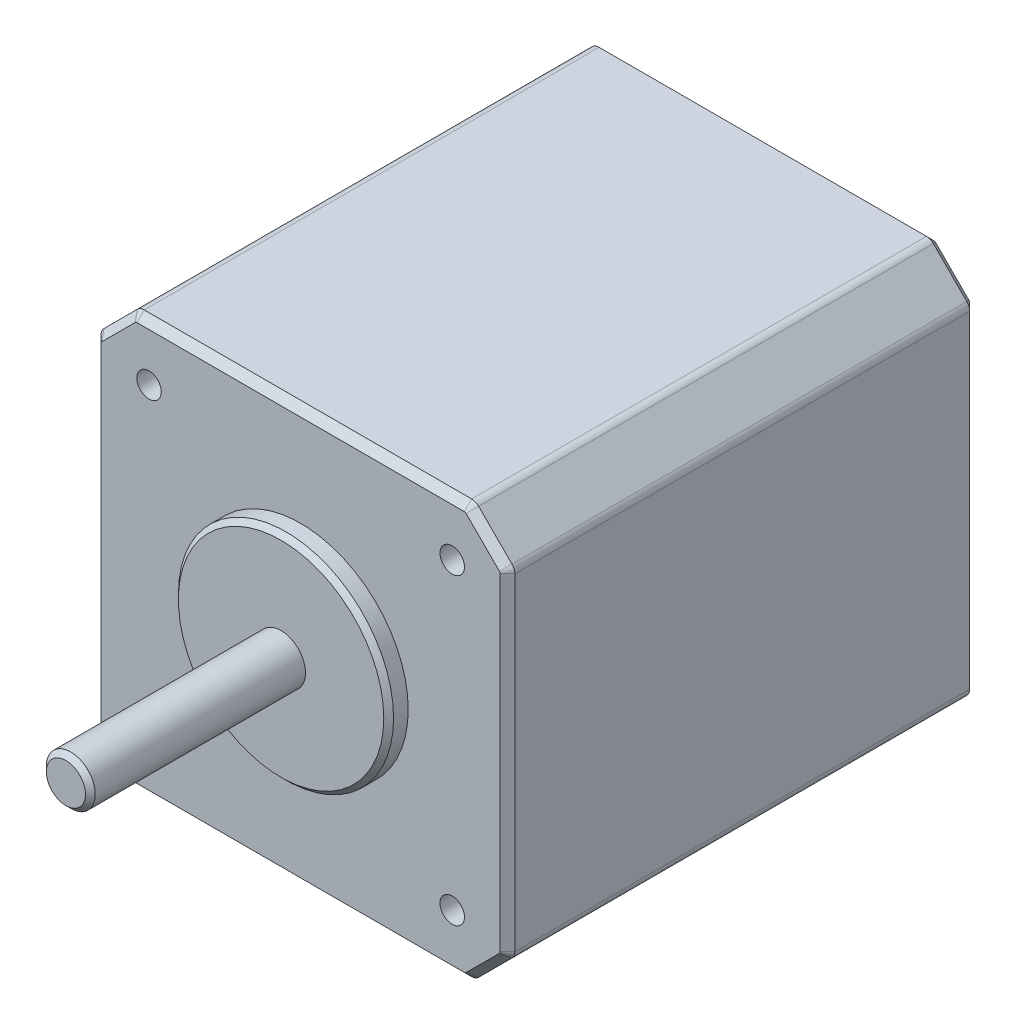
SolidWorks part; units mm, degrees
ref_plane "Спереди" through (0, 0, 0) normal (0, 0, 1) x (1, 0, 0)
ref_plane "Сверху" through (0, 0, 0) normal (0, 1, 0) x (1, 0, 0)
ref_plane "Справа" through (0, 0, 0) normal (1, 0, 0) x (0, 0, -1)
sketch "Sketch1" plane through (0, 0, 0) normal (0, 0, 1) x (1, 0, 0)
  line L1 (-21.15, -21.15) -> (21.15, -21.15)
  line L2 (-21.15, -21.15) -> (-21.15, 21.15)
  line L3 (-21.15, 21.15) -> (21.15, 21.15)
  line L4 (21.15, -21.15) -> (21.15, 21.15)
  line L5 (-21.15, -21.15) -> (21.15, 21.15) construction
  line L6 (-21.15, 21.15) -> (21.15, -21.15) construction
  line L11 (-15.5, -15.5) -> (15.5, 15.5) construction
  line L12 (-15.5, 15.5) -> (15.5, -15.5) construction
  point P0 (0, 0)
  point P6 (0, 0)
  point P12 (-15.5, 15.5)
  point P13 (15.5, 15.5)
  point P14 (15.5, -15.5)
  point P15 (-15.5, -15.5)
extrude "Boss-Extrude1" add sketch "Sketch1" against normal blind 48
hole_wizard "M3x0.5 Tapped Hole1" positions "Sketch5" profile "Sketch4" tap size "M3x0.5" standard "ANSI Metric"
sketch "Sketch5" plane through (0, 0, 0) normal (0, 0, 1) x (1, 0, 0)
  point P0 (-15.5, 15.5)
  point P3 (15.5, 15.5)
  point P6 (15.5, -15.5)
  point P9 (-15.5, -15.5)
sketch "Sketch4" plane through (-15.5, 15.5, 0) normal (1, 0, 0) x (0, -1, 0)
  line L0 (0, 0) -> (0, 6.7511)
  line L1 (0, 6.7511) -> (1.25, 6)
  line L2 (1.25, 6) -> (1.25, 0)
  line L5 (1.25, 0) -> (0, 0)
  line L10 (0, 6.7511) -> (-1.25, 6) construction
  line L11 (0, -6.35) -> (0, 107.95) construction
  dimension "Tap Drill Dia." = 2.5
  dimension "Tap Drill Depth" = 6
  dimension "Drill Angle" = 118
cosmetic thread "Hole Thread1" parameters "D1"=4.5, "D2"=3
cosmetic thread "Hole Thread2" parameters "D1"=4.5, "D2"=3
cosmetic thread "Hole Thread3" parameters "D1"=4.5, "D2"=3
cosmetic thread "Hole Thread4" parameters "D1"=4.5, "D2"=3
chamfer "Chamfer1" distance 4 angle 45 4 edges at (-21.15, -21.15, -24) (21.15, -21.15, -24) (21.15, 21.15, -24) (-21.15, 21.15, -24)
fillet "Fillet1" radius 1 8 edges at (-21.15, -17.15, -24) (-17.15, -21.15, -24) (17.15, -21.15, -24) (21.15, -17.15, -24) (21.15, 17.15, -24) (17.15, 21.15, -24) (-17.15, 21.15, -24) (-21.15, 17.15, -24)
sketch "Sketch6" plane through (0, 0, 0) normal (0, 0, 1) x (1, 0, 0)
  circle A0 centre (0, 0) radius 11
extrude "Boss-Extrude2" add sketch "Sketch6" along normal blind 2
sketch "Sketch7" plane through (0, 0, 2) normal (0, 0, 1) x (1, 0, 0)
  line L0 (-21.15, -21.15) -> (21.15, 21.15) construction
  circle A0 centre (0, 0) radius 2.5
extrude "Boss-Extrude3" add sketch "Sketch7" along normal blind 22
chamfer "Chamfer2" distance 0.5 angle 45 1 edges at (2.5, 0, 24)
chamfer "Chamfer3" distance 0.75 angle 45 16 edges at (0, -21.15, 0) (17.1185, -21.0739, 0) (-17.1185, -21.0739, 0) (19.15, -19.15, 0) (-19.15, -19.15, 0) (21.0739, -17.1185, 0) (-21.0739, -17.1185, 0) (21.15, 0, 0) (-21.15, 0, 0) (21.0739, 17.1185, 0) (-21.0739, 17.1185, 0) (19.15, 19.15, 0) (-19.15, 19.15, 0) (17.1185, 21.0739, 0) (-17.1185, 21.0739, 0) (0, 21.15, 0)
chamfer "Chamfer4" distance 0.5 angle 45 1 edges at (11, 0, 2)
chamfer "Chamfer6" distance 0.75 angle 45 16 edges at (0, -21.15, -48) (17.1185, -21.0739, -48) (-17.1185, -21.0739, -48) (19.15, -19.15, -48) (-19.15, -19.15, -48) (21.0739, -17.1185, -48) (-21.0739, -17.1185, -48) (21.15, 0, -48) (-21.15, 0, -48) (21.0739, 17.1185, -48) (-21.0739, 17.1185, -48) (19.15, 19.15, -48) (-19.15, 19.15, -48) (17.1185, 21.0739, -48) (-17.1185, 21.0739, -48) (0, 21.15, -48)
